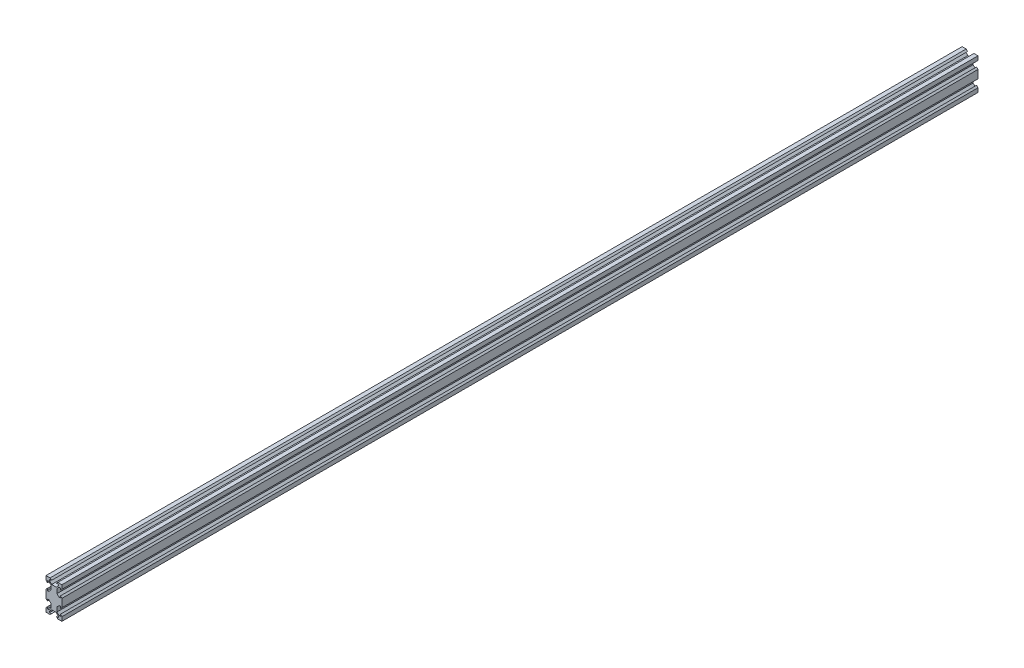
SolidWorks part; units mm, degrees
ref_plane "Front Plane" through (0, 0, 0) normal (0, 0, 1) x (1, 0, 0)
ref_plane "Top Plane" through (0, 0, 0) normal (0, 1, 0) x (1, 0, 0)
ref_plane "Right Plane" through (0, 0, 0) normal (1, 0, 0) x (0, 0, -1)
sketch "Sketch1" plane through (0, 0, 0) normal (0, 0, 1) x (1, 0, 0)
  line L1 (0, 0) -> (20, 0)
  line L2 (0, 0) -> (0, 40)
  line L3 (0, 40) -> (20, 40)
  line L4 (20, 0) -> (20, 40)
  line L5 (0, 0) -> (20, 40) construction
  line L6 (0, 40) -> (20, 0) construction
  point P4 (10, 20)
  dimension "D1" = 20
  dimension "D2" = 40
extrude "Boss-Extrude1" add sketch "Sketch1" along normal blind 1153.3
sketch "Sketch2" plane through (0, 0, 1153.3) normal (0, 0, 1) x (1, 0, 0)
  line L0 (5.12, 40) -> (6.94, 38.18)
  line L1 (20, 40) -> (0, 40) construction
  line L3 (13.06, 38.18) -> (14.88, 40)
  line L4 (0, 40) -> (20, 40) construction
  line L5 (20, 40) -> (10, 40) construction
  line L6 (10, 40) -> (10, 38.18) construction
  line L7 (5.12, 40) -> (14.88, 40)
  line L8 (6.94, 38.18) -> (4.5, 38.18)
  line L9 (4.5, 38.18) -> (4.5, 36.4758)
  line L10 (4.5, 36.4758) -> (7.1658, 33.81)
  line L11 (7.1658, 33.81) -> (12.8342, 33.81)
  line L12 (12.8342, 33.81) -> (15.5, 36.4758)
  line L13 (15.5, 36.4758) -> (15.5, 38.18)
  line L14 (15.5, 38.18) -> (13.06, 38.18)
  line L15 (20, 40) -> (0, 20) construction
  line L16 (0, 40) -> (0, 0) construction
  line L17 (20, 30) -> (18.18, 30) construction
  line L18 (18.18, 35.5) -> (18.18, 33.06)
  line L19 (16.4758, 35.5) -> (18.18, 35.5)
  line L20 (13.81, 32.8342) -> (16.4758, 35.5)
  line L21 (13.81, 27.1658) -> (13.81, 32.8342)
  line L22 (16.4758, 24.5) -> (13.81, 27.1658)
  line L23 (18.18, 24.5) -> (16.4758, 24.5)
  line L24 (18.18, 26.94) -> (18.18, 24.5)
  line L25 (20, 25.12) -> (20, 34.88)
  line L26 (18.18, 33.06) -> (20, 34.88)
  line L28 (20, 25.12) -> (18.18, 26.94)
  line L29 (0, 20) -> (20, 20) construction
  line L30 (20, 0) -> (20, 40) construction
  line L31 (20, 10) -> (18.18, 10) construction
  line L32 (10, 0) -> (10, 1.82) construction
  line L33 (20, 0) -> (10, 0) construction
  line L34 (20, 14.88) -> (18.18, 13.06)
  line L36 (18.18, 6.94) -> (20, 5.12)
  line L37 (20, 14.88) -> (20, 5.12)
  line L38 (18.18, 13.06) -> (18.18, 15.5)
  line L39 (18.18, 15.5) -> (16.4758, 15.5)
  line L40 (16.4758, 15.5) -> (13.81, 12.8342)
  line L41 (13.81, 12.8342) -> (13.81, 7.1658)
  line L42 (13.81, 7.1658) -> (16.4758, 4.5)
  line L43 (16.4758, 4.5) -> (18.18, 4.5)
  line L44 (18.18, 4.5) -> (18.18, 6.94)
  line L45 (15.5, 1.82) -> (13.06, 1.82)
  line L46 (15.5, 3.5242) -> (15.5, 1.82)
  line L47 (12.8342, 6.19) -> (15.5, 3.5242)
  line L48 (7.1658, 6.19) -> (12.8342, 6.19)
  line L49 (4.5, 3.5242) -> (7.1658, 6.19)
  line L50 (4.5, 1.82) -> (4.5, 3.5242)
  line L51 (6.94, 1.82) -> (4.5, 1.82)
  line L52 (5.12, 0) -> (14.88, 0)
  line L53 (13.06, 1.82) -> (14.88, 0)
  line L55 (5.12, 0) -> (6.94, 1.82)
  line L56 (10, 40) -> (10, 0) construction
  line L57 (0, 10) -> (1.82, 10) construction
  line L58 (0, 30) -> (1.82, 30) construction
  line L59 (1.82, 4.5) -> (1.82, 6.94)
  line L60 (3.5242, 4.5) -> (1.82, 4.5)
  line L61 (6.19, 7.1658) -> (3.5242, 4.5)
  line L62 (6.19, 12.8342) -> (6.19, 7.1658)
  line L63 (3.5242, 15.5) -> (6.19, 12.8342)
  line L64 (1.82, 15.5) -> (3.5242, 15.5)
  line L65 (1.82, 13.06) -> (1.82, 15.5)
  line L66 (0, 14.88) -> (0, 5.12)
  line L67 (1.82, 6.94) -> (0, 5.12)
  line L69 (0, 14.88) -> (1.82, 13.06)
  line L70 (0, 25.12) -> (1.82, 26.94)
  line L72 (1.82, 33.06) -> (0, 34.88)
  line L73 (0, 25.12) -> (0, 34.88)
  line L74 (1.82, 26.94) -> (1.82, 24.5)
  line L75 (1.82, 24.5) -> (3.5242, 24.5)
  line L76 (3.5242, 24.5) -> (6.19, 27.1658)
  line L77 (6.19, 27.1658) -> (6.19, 32.8342)
  line L78 (6.19, 32.8342) -> (3.5242, 35.5)
  line L79 (3.5242, 35.5) -> (1.82, 35.5)
  line L80 (1.82, 35.5) -> (1.82, 33.06)
  dimension "D1" = 90
  dimension "D3" = 6.12
  dimension "D5" = 11
  dimension "D6" = 6.19
  dimension "D7" = 1.38
extrude "Cut-Extrude1" cut sketch "Sketch2" against normal through all
